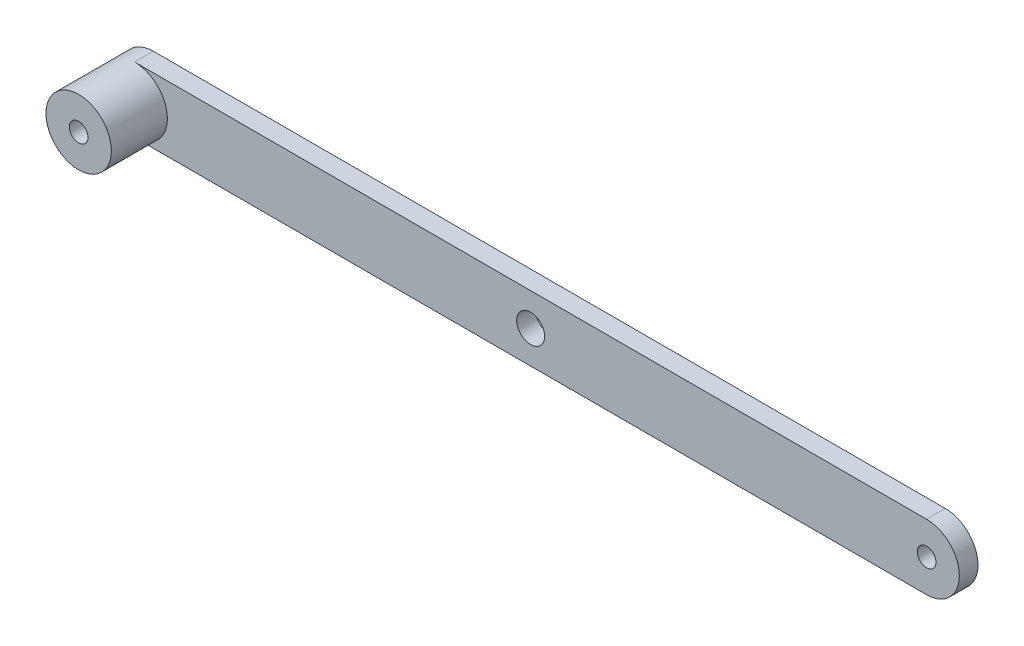
SolidWorks part; units mm, degrees
ref_plane "Alzado" through (0, 0, 0) normal (0, 0, 1) x (1, 0, 0)
ref_plane "Planta" through (0, 0, 0) normal (0, 1, 0) x (1, 0, 0)
ref_plane "Vista lateral" through (0, 0, 0) normal (1, 0, 0) x (0, 0, -1)
sketch "Croquis1" plane through (0, 0, 0) normal (0, 0, 1) x (1, 0, 0)
  line L0 (-212, 0) -> (212, 0) construction
  line L1 (-212, 17.5) -> (212, 17.5)
  line L2 (-212, -17.5) -> (212, -17.5)
  arc A0 (-212, 17.5) -> (-212, -17.5) centre (-212, 0) ccw
  arc A1 (212, -17.5) -> (212, 17.5) centre (212, 0) ccw
  circle A2 centre (-212, 0) radius 5
  circle A3 centre (212, 0) radius 5
  circle A4 centre (0, 0) radius 7.5
  point P2 (0, 0)
  dimension "D2" = 17.5
  dimension "D3" = 10
  dimension "D4" = 10
  dimension "D5" = 15
  dimension "D1" = 424
extrude "Saliente-Extruir1" add sketch "Croquis1" along normal blind 10
sketch "Croquis2" plane through (0, 0, 10) normal (0, 0, 1) x (1, 0, 0)
  circle A0 centre (-212, 0) radius 17.5
  circle A1 centre (-212, 0) radius 5
extrude "Saliente-Extruir2" add sketch "Croquis2" along normal blind 30
